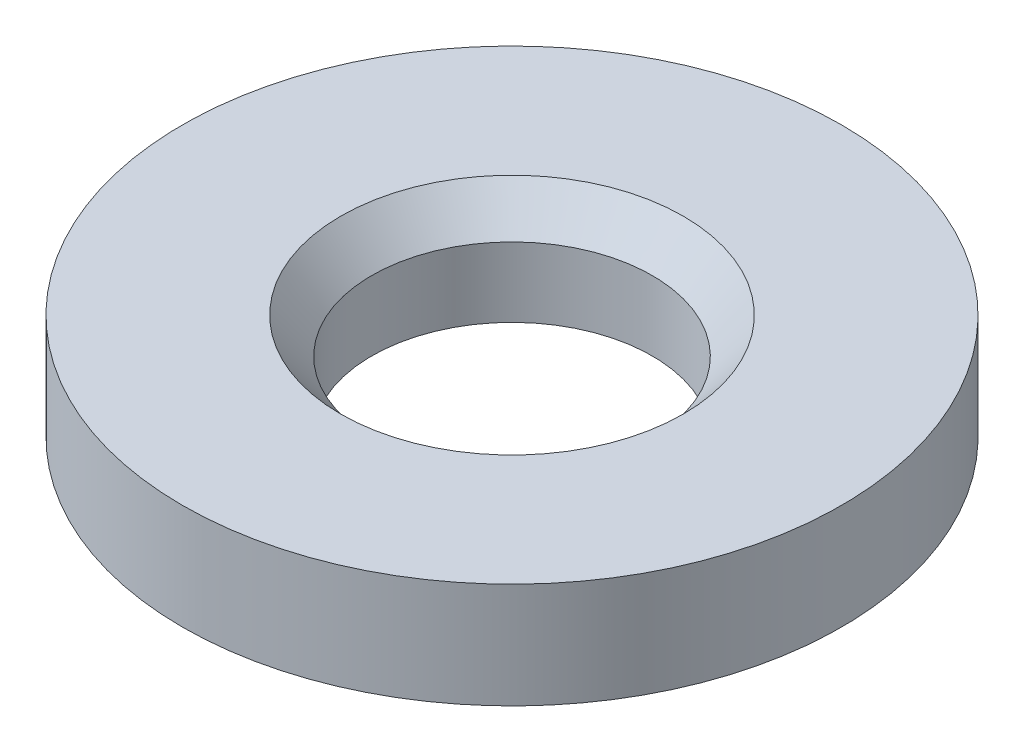
SolidWorks part; units mm, degrees
material "PET"
ref_plane "Front Plane" through (0, 0, 0) normal (0, 0, 1) x (1, 0, 0)
ref_plane "Top Plane" through (0, 0, 0) normal (0, 1, 0) x (1, 0, 0)
ref_plane "Right Plane" through (0, 0, 0) normal (1, 0, 0) x (0, 0, -1)
sketch "Sketch2" plane through (0, 0, 0) normal (0, 1, 0) x (1, 0, 0)
  circle A0 centre (0, 0) radius 7.9375
  dimension "D1" = 15.875
extrude "Boss-Extrude1" add sketch "Sketch2" along normal blind 2.54
sketch "Sketch3" plane through (0, 2.54, 0) normal (0, 1, 0) x (1, 0, 0)
  point P0 (0, 0)
hole_wizard "CSK for #10 Flat Head Machine Screw (100)1" positions "Sketch3" profile "Sketch5" countersink size "#10" standard "ANSI Inch" end condition through all
sketch "Sketch5" plane through (0, 2.54, 0) normal (1, 0, 0) x (0, 0, 1)
  line L0 (0, 0) -> (0, 2.54)
  line L1 (0, 2.54) -> (3.3782, 2.54)
  line L2 (3.3782, 2.54) -> (3.3782, 0.862)
  line L3 (3.3782, 0.862) -> (4.1275, 0)
  line L5 (4.1275, 0) -> (0, 0)
  line L6 (-3.3782, 0.862) -> (-4.1275, 0) construction
  line L11 (0, -6.35) -> (0, 107.95) construction
  dimension "Thru Hole Dia." = 6.7564
  dimension "Thru Hole Depth" = 2.54
  dimension "Near C'Sink Dia." = 8.255
  dimension "Near C'Sink Angle" = 82
